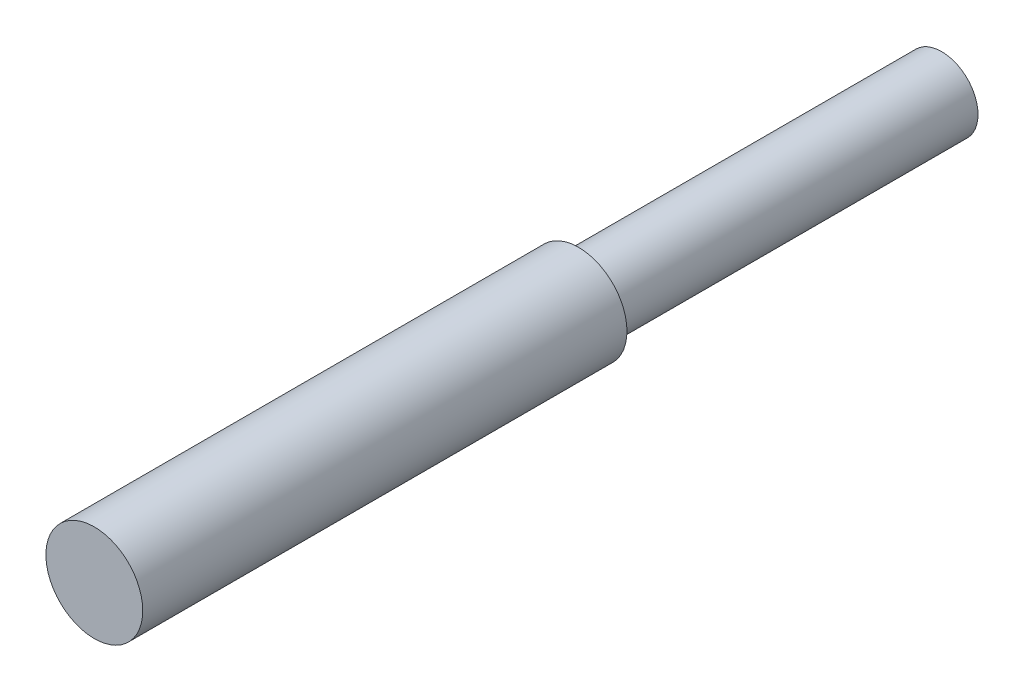
SolidWorks part; units mm, degrees
ref_plane "Front Plane" through (0, 0, 0) normal (0, 0, 1) x (1, 0, 0)
ref_plane "Top Plane" through (0, 0, 0) normal (0, 1, 0) x (1, 0, 0)
ref_plane "Right Plane" through (0, 0, 0) normal (1, 0, 0) x (0, 0, -1)
sketch "Sketch1" plane through (0, 0, 0) normal (0, 0, 1) x (1, 0, 0)
  circle A0 centre (0, 0) radius 15
  dimension "D1" = 30
extrude "Boss-Extrude1" add sketch "Sketch1" along normal blind 150
sketch "Sketch2" plane through (0, 0, 150) normal (0, 0, 1) x (1, 0, 0)
  circle A0 centre (0, 0) radius 20
  dimension "D1" = 40
extrude "Boss-Extrude2" add sketch "Sketch2" along normal blind 200
